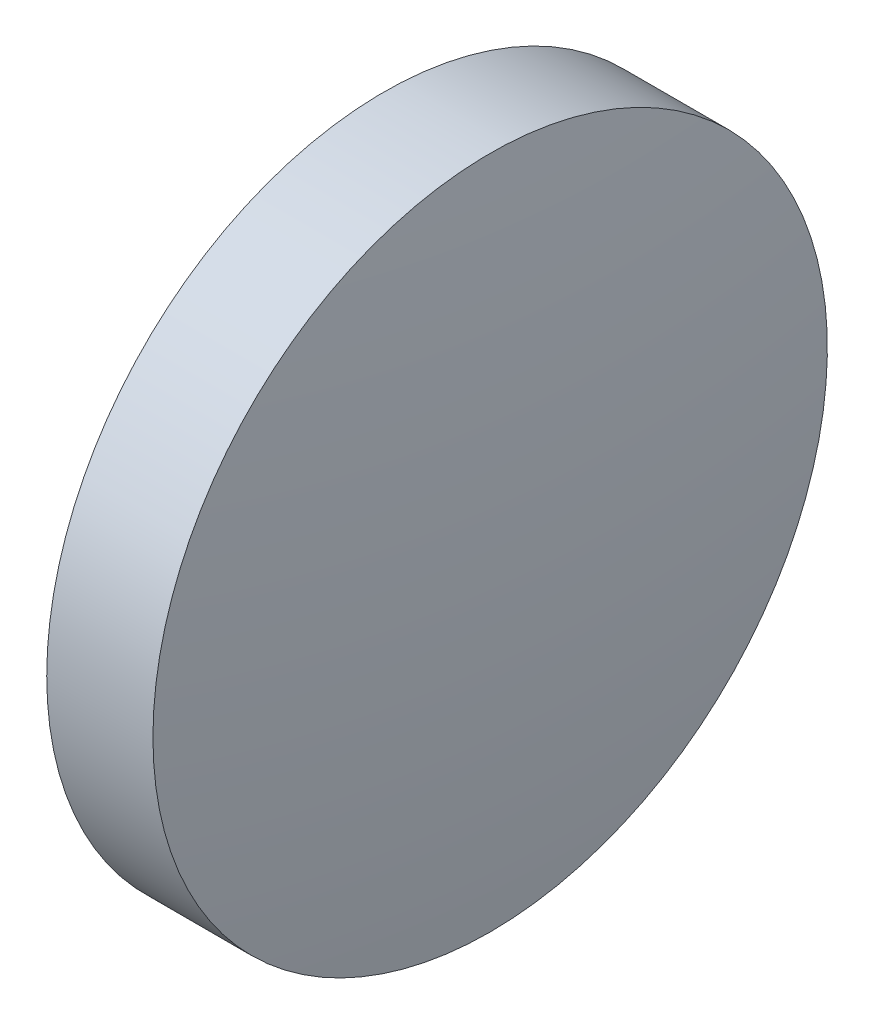
SolidWorks part; units mm, degrees
ref_plane "前视基准面" through (0, 0, 0) normal (0, 0, 1) x (1, 0, 0)
ref_plane "上视基准面" through (0, 0, 0) normal (0, 1, 0) x (1, 0, 0)
ref_plane "右视基准面" through (0, 0, 0) normal (1, 0, 0) x (0, 0, -1)
sketch "草图2" plane through (0, 0, 0) normal (0, 0, 1) x (1, 0, 0)
  line L0 (549.552, 54.8275) -> (557.0704, 54.8275) construction
  line L1 (551.8126, 54.8275) -> (551.8126, 61.1775)
  line L2 (554.2126, 54.8275) -> (551.8126, 54.8275)
  line L5 (551.8126, 61.1775) -> (553.8126, 61.1775)
  arc A0 (554.2126, 54.8275) -> (553.8126, 61.1775) centre (503.6094, 54.8275) ccw
revolve "旋转2" add sketch "草图2" angle 360 about L0
